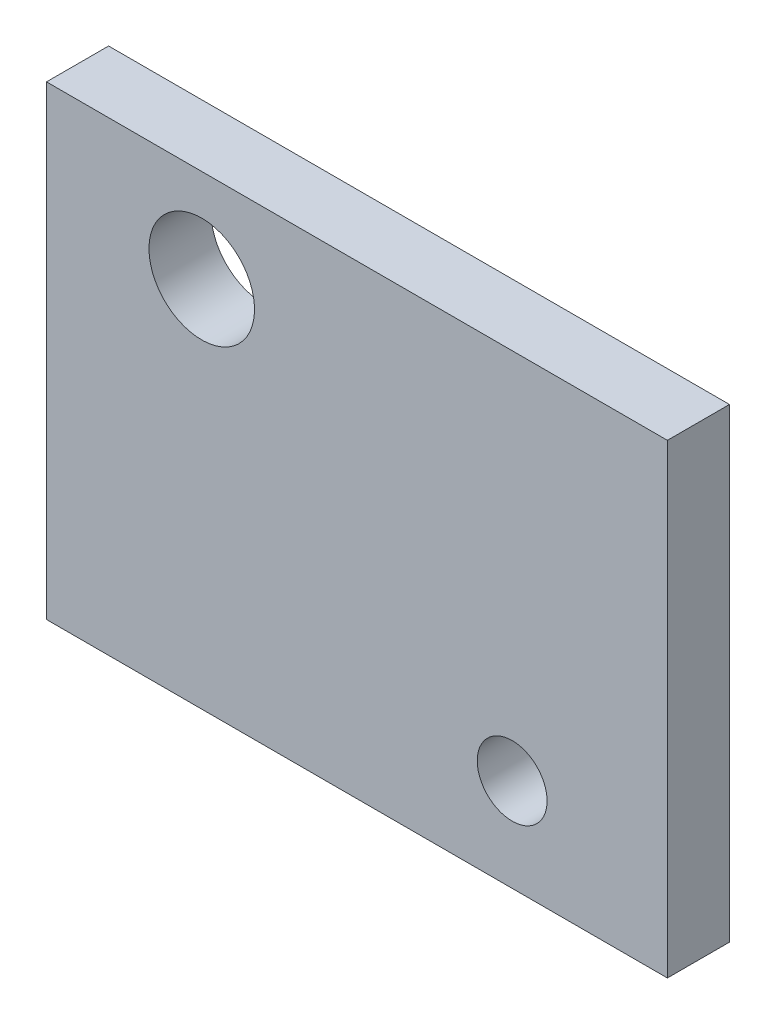
SolidWorks part; units mm, degrees
ref_plane "Front Plane" through (0, 0, 0) normal (0, 0, 1) x (1, 0, 0)
ref_plane "Top Plane" through (0, 0, 0) normal (0, 1, 0) x (1, 0, 0)
ref_plane "Right Plane" through (0, 0, 0) normal (1, 0, 0) x (0, 0, -1)
sketch "Sketch1" plane through (0, 0, 0) normal (0, 0, 1) x (1, 0, 0)
  line L1 (-100, -75) -> (100, -75)
  line L2 (-100, -75) -> (-100, 75)
  line L3 (-100, 75) -> (100, 75)
  line L4 (100, -75) -> (100, 75)
  line L5 (-100, -75) -> (100, 75) construction
  line L6 (-100, 75) -> (100, -75) construction
  point P0 (0, 0)
  dimension "D1" = 200
  dimension "D2" = 150
extrude "Boss-Extrude1" add sketch "Sketch1" along normal blind 20
sketch "Sketch2" plane through (0, 0, 0) normal (0, 0, -1) x (-1, 0, 0)
  line L0 (-100, -75) -> (-100, 75) construction
  line L1 (100, -75) -> (-100, -75) construction
  line L2 (50, 45) -> (26.6293, 45) construction
  line L3 (50, 45) -> (50, 79.3134) construction
  circle A0 centre (-50, -45) radius 11.25
  circle A1 centre (50, 45) radius 17
  dimension "D1" = 22.5
  dimension "D2" = 34
  dimension "D3" = 50
  dimension "D4" = 30
  dimension "D5" = 90
  dimension "D6" = 100
extrude "Cut-Extrude1" cut sketch "Sketch2" against normal through all
